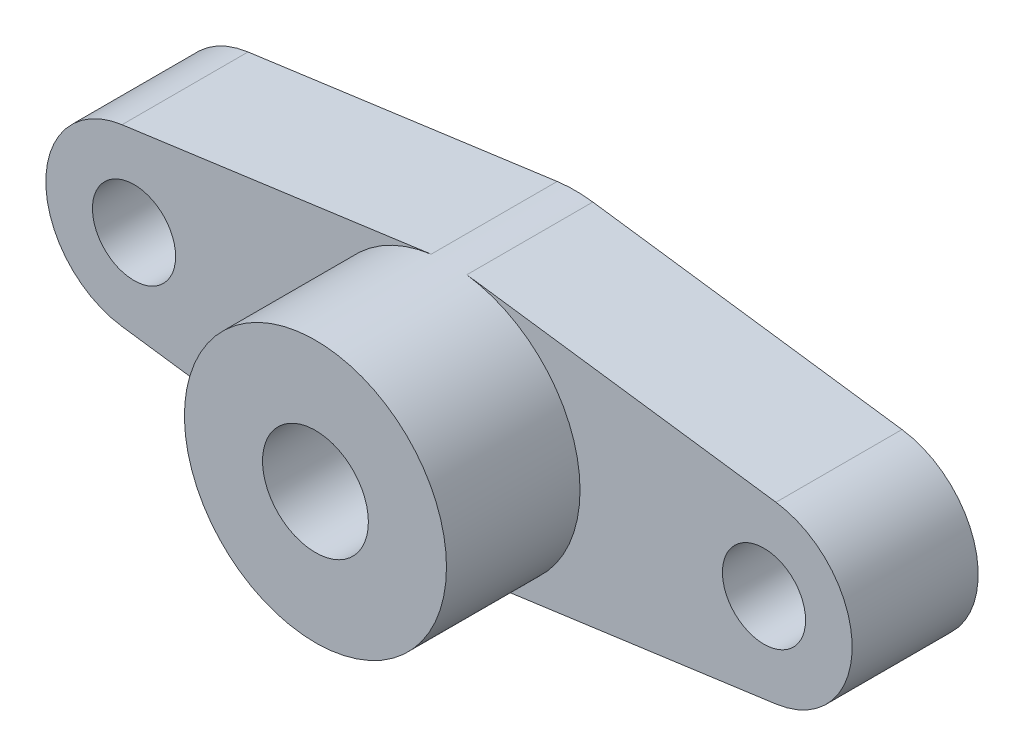
SolidWorks part; units mm, degrees
material "1060 合金"
ref_plane "前视基准面" through (0, 0, 0) normal (0, 0, 1) x (1, 0, 0)
ref_plane "上视基准面" through (0, 0, 0) normal (0, 1, 0) x (1, 0, 0)
ref_plane "右视基准面" through (0, 0, 0) normal (1, 0, 0) x (0, 0, -1)
other "Configuration Table"
sketch "草图1" plane through (0, 0, 0) normal (0, 0, 1) x (1, 0, 0)
  line L0 (-12.5, 0) -> (12.5, 0) construction
  line L2 (-16, -5.2) -> (16, -5.2)
  line L3 (-16, -5.2) -> (-16, 5.2)
  line L4 (-16, 5.2) -> (16, 5.2)
  line L5 (16, -5.2) -> (16, 5.2)
  line L6 (-16, -5.2) -> (16, 5.2) construction
  line L7 (-16, 5.2) -> (16, -5.2) construction
  circle A0 centre (-12.5, 0) radius 0.5
  circle A1 centre (12.5, 0) radius 0.5
  circle A2 centre (0, 0) radius 0.5
  circle A3 centre (-12.5, 0) radius 3.5 construction
  point P4 (0, 0)
  dimension "D1" = 1
  dimension "D2" = 1
  dimension "D4" = 5.2
  dimension "D5" = 7
  dimension "D3" = 25
extrude "凸台-拉伸1" add sketch "草图1" along normal blind 5
sketch "草图2" plane through (0, 0, 5) normal (0, 0, 1) x (1, 0, 0)
  line L0 (16, 5.2) -> (-16, 5.2) construction
  circle A0 centre (0, 0) radius 0.5
  circle A1 centre (0, 0) radius 5.2
  circle A2 centre (0, 0) radius 2.5 construction
  dimension "D1" = 1
  dimension "D3" = 5
extrude "凸台-拉伸2" add sketch "草图2" along normal blind 5.3 contours A1 A2
sketch "草图3" plane through (0, 0, 5) normal (0, 0, 1) x (1, 0, 0)
  line L0 (-16, 5.2) -> (-16, -5.2) construction
  line L1 (-0.7072, 5.1517) -> (-12.976, 3.4675)
  line L2 (-12.976, -3.4675) -> (-0.7072, -5.1517)
  line L3 (0.7072, 5.1517) -> (12.976, 3.4675)
  line L4 (0.7072, -5.1517) -> (12.976, -3.4675)
  line L6 (-16, 5.2) -> (16, 5.2)
  line L7 (-16, 5.2) -> (-16, -5.2)
  line L8 (-16, -5.2) -> (16, -5.2)
  line L9 (16, 5.2) -> (16, -5.2)
  circle A0 centre (0, 0) radius 5.2
  circle A2 centre (12.5, 0) radius 3.5
  circle A3 centre (-12.5, 0) radius 3.5
  circle A4 centre (0, 0) radius 5.2 construction
  arc M3 (0, -5.2) -> (0, 5.2) centre (0, 0) cw
  line M4 (0, 5.2) -> (-16, 5.2)
  line M5 (-16, 5.2) -> (-16, -5.2)
  line M6 (-16, -5.2) -> (0, -5.2)
extrude "切除-拉伸1" cut sketch "草图3" against normal blind 5.3 contours A3 L1 M3 M4 M5 | A3 L7 L2 M6 M3 | A2 L4 A0 L8 L9 | A2 L9 L6 A0 L3
hole_wizard "M4 螺纹孔1" positions "草图4" profile "草图5" tap size "M4" standard "GB"
sketch "草图4" plane through (0, 0, 5) normal (0, 0, 1) x (1, 0, 0)
  point P0 (-12.5, 0)
  point P3 (12.5, 0)
sketch "草图5" plane through (-12.5, 0, 5) normal (1, 0, 0) x (0, -1, 0)
  line L0 (0, 0) -> (0, 11.0914)
  line L1 (0, 11.0914) -> (1.65, 10.1)
  line L2 (1.65, 10.1) -> (1.65, 0)
  line L5 (1.65, 0) -> (0, 0)
  line L10 (0, 11.0914) -> (-1.65, 10.1) construction
  line L11 (0, -6.35) -> (0, 107.95) construction
  dimension "螺纹孔钻头直径" = 3.3
  dimension "螺纹孔钻头深度" = 10.1
  dimension "导头角度" = 118
cosmetic thread "孔螺蚊线1" parameters "D1"=8, "D2"=4
cosmetic thread "孔螺蚊线2" parameters "D1"=8, "D2"=4
hole_wizard "M5 螺纹孔1" positions "草图6" profile "草图7" tap size "M5" standard "GB"
sketch "草图6" plane through (0, 0, 10.3) normal (0, 0, 1) x (1, 0, 0)
  point P0 (0, 0)
sketch "草图7" plane through (0, 0, 10.3) normal (1, 0, 0) x (0, -1, 0)
  line L0 (0, 0) -> (0, 23.6618)
  line L1 (0, 23.6618) -> (2.1, 22.4)
  line L2 (2.1, 22.4) -> (2.1, 0)
  line L5 (2.1, 0) -> (0, 0)
  line L10 (0, 23.6618) -> (-2.1, 22.4) construction
  line L11 (0, -6.35) -> (0, 107.95) construction
  dimension "螺纹孔钻头直径" = 4.2
  dimension "螺纹孔钻头深度" = 22.4
  dimension "导头角度" = 118
cosmetic thread "孔螺蚊线3" parameters "D1"=20, "D2"=5
